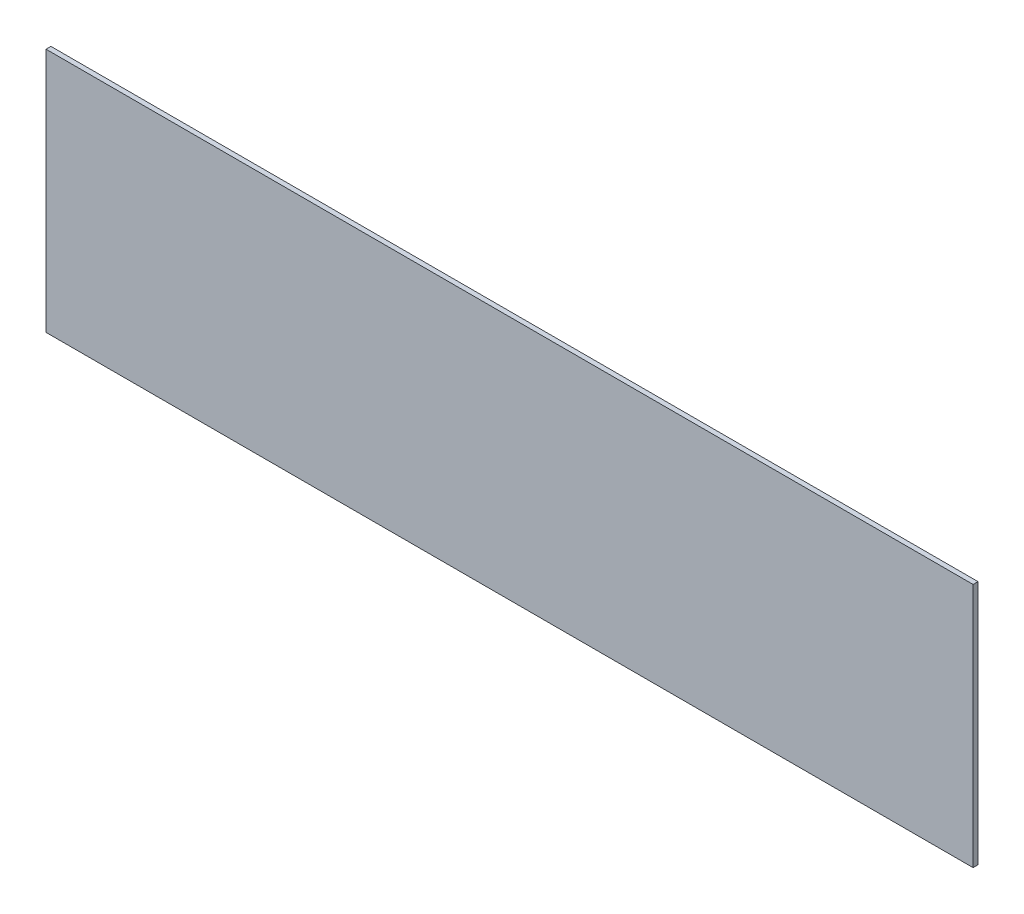
SolidWorks part; units mm, degrees
ref_plane "Front Plane" through (0, 0, 0) normal (0, 0, 1) x (1, 0, 0)
ref_plane "Top Plane" through (0, 0, 0) normal (0, 1, 0) x (1, 0, 0)
ref_plane "Right Plane" through (0, 0, 0) normal (1, 0, 0) x (0, 0, -1)
sketch "Sketch1" plane through (0, 0, 0) normal (0, 0, 1) x (1, 0, 0)
  line L1 (-62.1495, 56.9229) -> (126.8505, 56.9229)
  line L2 (-62.1495, 56.9229) -> (-62.1495, 6.9229)
  line L3 (-62.1495, 6.9229) -> (126.8505, 6.9229)
  line L4 (126.8505, 56.9229) -> (126.8505, 6.9229)
  dimension "D1" = 50
  dimension "D2" = 189
extrude "Boss-Extrude1" add sketch "Sketch1" along normal blind 1
